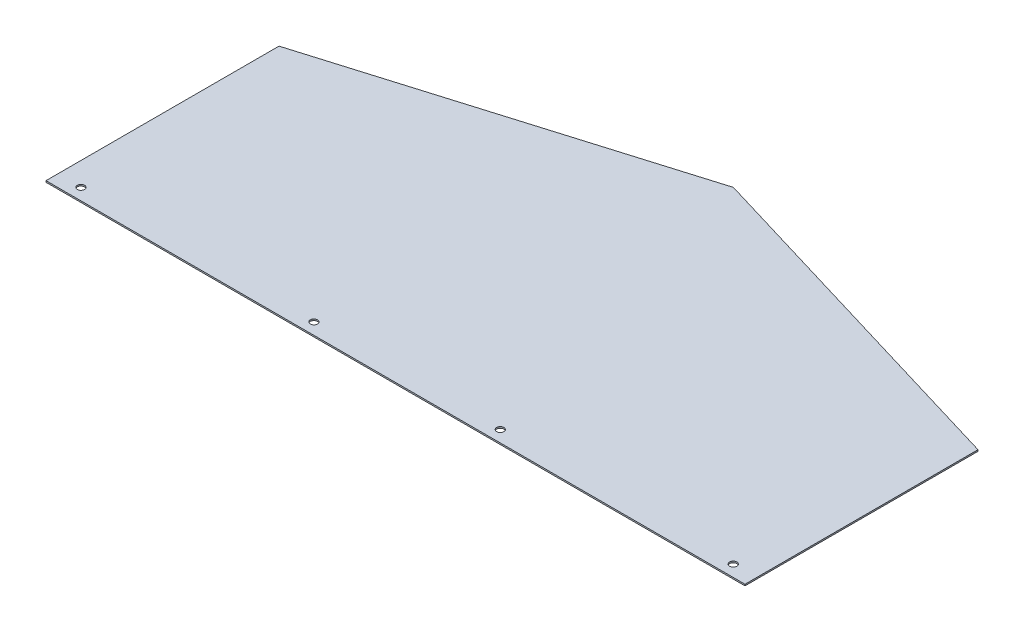
SolidWorks part; units mm, degrees
ref_plane "Front Plane" through (0, 0, 0) normal (0, 0, 1) x (1, 0, 0)
ref_plane "Top Plane" through (0, 0, 0) normal (0, 1, 0) x (1, 0, 0)
ref_plane "Right Plane" through (0, 0, 0) normal (1, 0, 0) x (0, 0, -1)
sketch "Sketch1" plane through (0, 0, 0) normal (0, 1, 0) x (1, 0, 0)
  line L0 (0, 0) -> (1524, 0)
  line L1 (0, 0) -> (0, 508)
  line L2 (1524, 0) -> (1524, 508)
  line L3 (0, 508) -> (762, 736.6)
  line L4 (762, 736.6) -> (1524, 508)
  dimension "D1" = 1524
  dimension "D2" = 508
  dimension "D3" = 736.6
extrude "Boss-Extrude1" add sketch "Sketch1" along normal blind 3.175
hole_wizard "5/8 (0.625) Diameter Hole1" positions "Sketch3" profile "Sketch2" hole size "5/8" standard "Ansi Inch" end condition up to next
sketch "Sketch3" plane through (0, 0, 0) normal (0, -1, 0) x (1, 0, 0)
  line L0 (0, 0) -> (1524, 0) construction
  line L1 (0, -508) -> (0, 0) construction
  line L2 (1524, 0) -> (1524, -508) construction
  line L3 (50.8, -25.4) -> (1524, -25.1853) construction
  point P0 (50.8, -25.4)
  point P1 (558.8, -25.326)
  point P3 (965.2, -25.2667)
  point P5 (1473.2, -25.1927)
  dimension "D1" = 25.4
  dimension "D2" = 508
  dimension "D3" = 50.8
  dimension "D4" = 406.4
  dimension "D5" = 508
sketch "Sketch2" plane through (50.8, 0, -25.4) normal (1, 0, 0) x (0, 0, -1)
  line L0 (0, 0) -> (0, 3.175)
  line L1 (0, 3.175) -> (7.9375, 3.175)
  line L2 (7.9375, 3.175) -> (7.9375, 0)
  line L5 (7.9375, 0) -> (0, 0)
  line L11 (0, -6.35) -> (0, 107.95) construction
  dimension "Thru Hole Dia." = 15.875
  dimension "Thru Hole Depth" = 3.175
